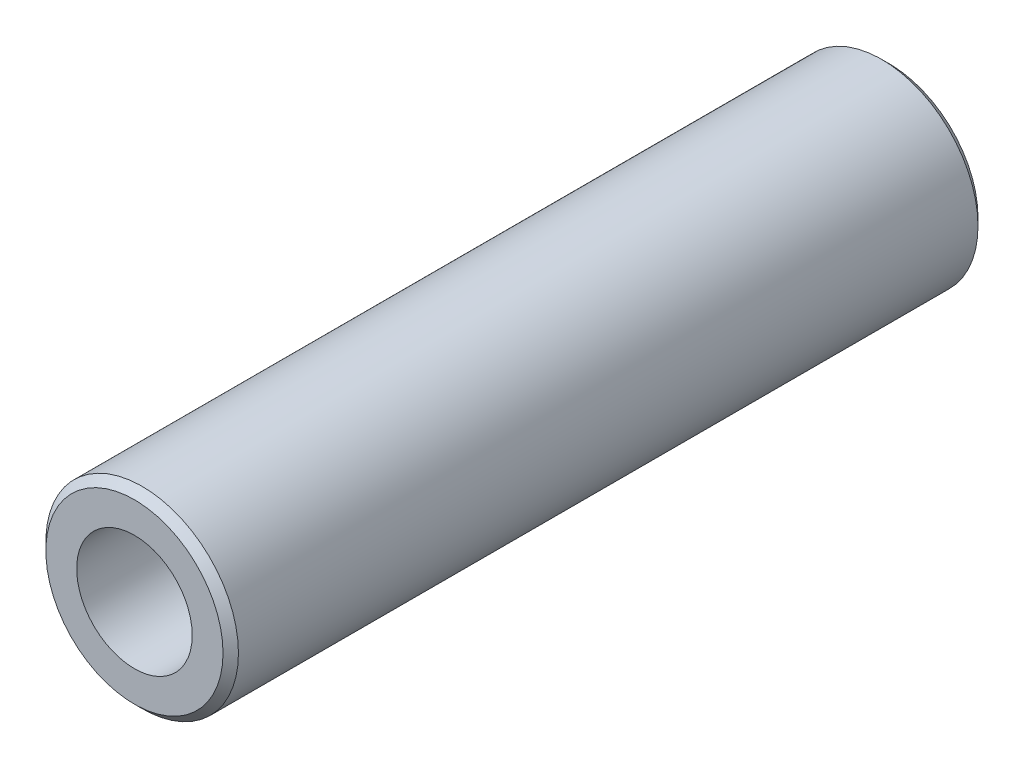
SolidWorks part; units mm, degrees
ref_plane "Front Plane" through (0, 0, 0) normal (0, 0, 1) x (1, 0, 0)
ref_plane "Top Plane" through (0, 0, 0) normal (0, 1, 0) x (1, 0, 0)
ref_plane "Right Plane" through (0, 0, 0) normal (1, 0, 0) x (0, 0, -1)
sketch "Sketch1" plane through (0, 0, 0) normal (0, 0, 1) x (1, 0, 0)
  circle A0 centre (0, 0) radius 158.75
  dimension "D1" = 317.5
extrude "Extrude-Thin1" add sketch "Sketch1" along normal blind 1244.6 thin thin type one direction reverse wall 63.5
chamfer "Chamfer1" distance 12.7 angle 45 2 edges at (158.75, 0, 0) (158.75, 0, 1244.6)
